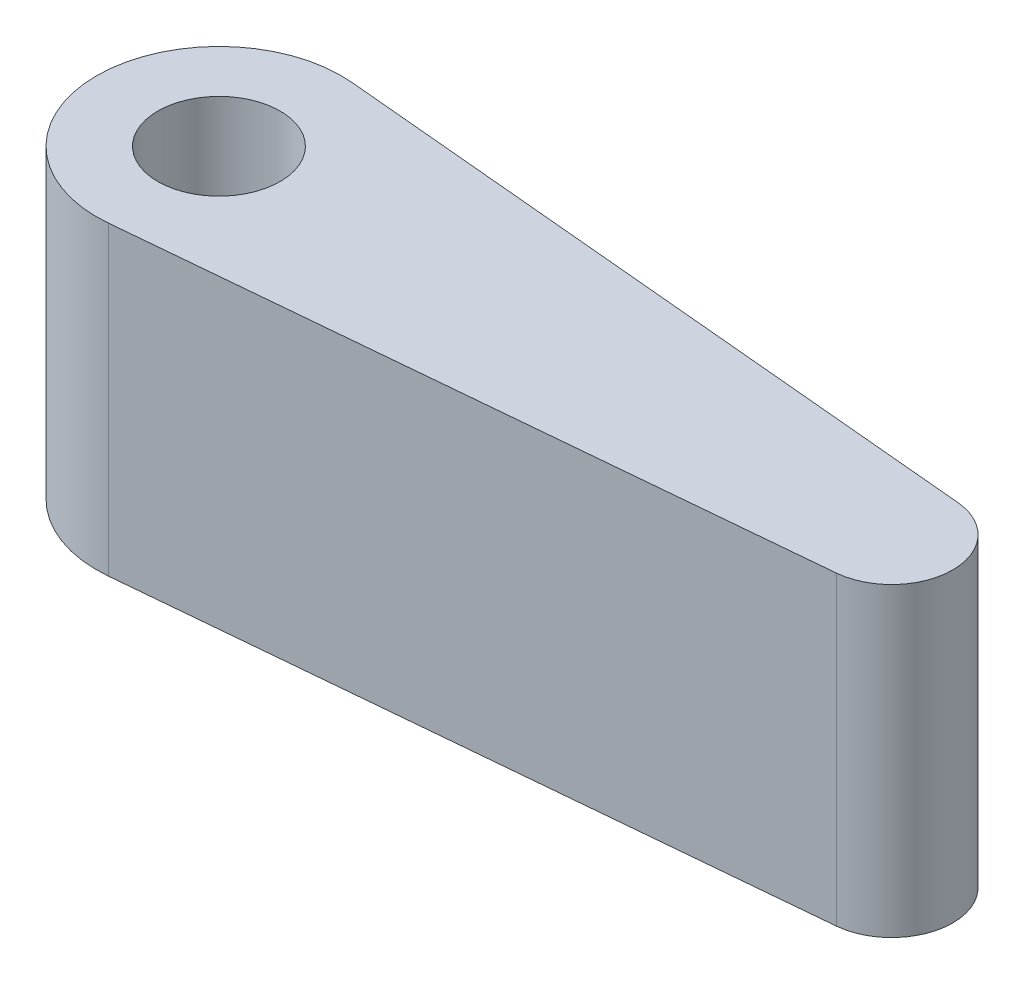
SolidWorks part; units mm, degrees
ref_plane "Front Plane" through (0, 0, 0) normal (0, 0, 1) x (1, 0, 0)
ref_plane "Top Plane" through (0, 0, 0) normal (0, 1, 0) x (1, 0, 0)
ref_plane "Right Plane" through (0, 0, 0) normal (1, 0, 0) x (0, 0, -1)
sketch "Sketch1" plane through (0, 0, 0) normal (0, 1, 0) x (1, 0, 0)
  line L0 (-24.0909, 9.9586) -> (30.4545, 4.9793)
  line L1 (-24.0909, -9.9586) -> (30.4545, -4.9793)
  line L2 (0, 23.8872) -> (0, -27.9037) construction
  line L3 (-58.7958, 0) -> (58.9975, 0) construction
  arc A0 (-24.0909, 9.9586) -> (-24.0909, -9.9586) centre (-25, 0) ccw
  arc A1 (30.4545, -4.9793) -> (30.4545, 4.9793) centre (30, 0) ccw
  circle A3 centre (-25, 0) radius 5
  point P1 (35, 0)
  dimension "D1" = 25
  dimension "R1" = 10
  dimension "D2" = 5
  dimension "D4" = 5
  dimension "D3" = 60
extrude "Boss-Extrude1" add sketch "Sketch1" along normal blind 25 contours A0 L1 A1 L0 | A3
